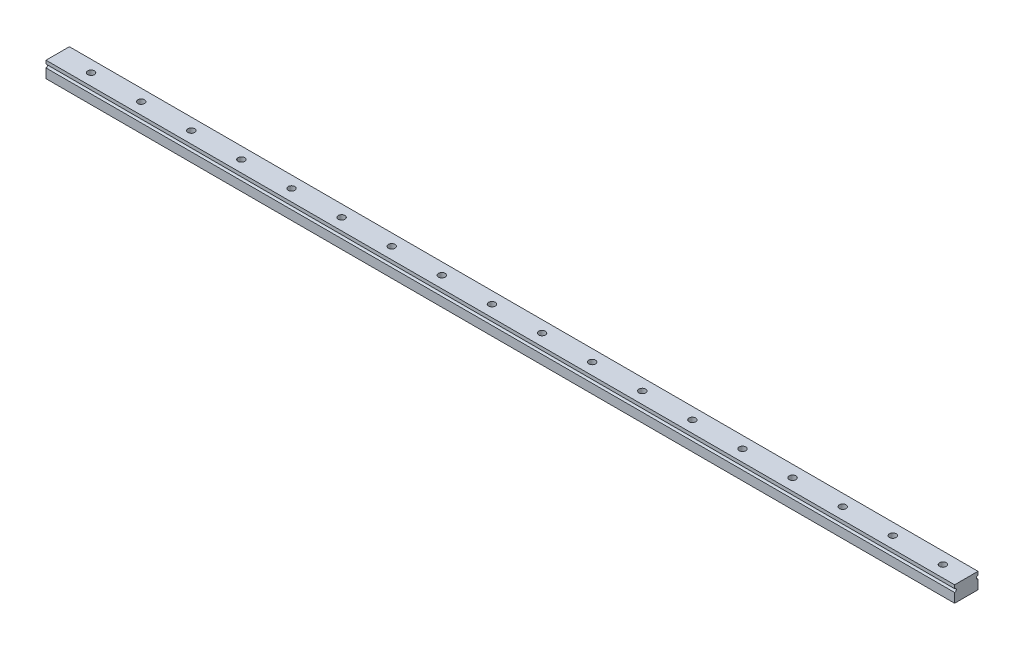
SolidWorks part; units mm, degrees
material "Plain Carbon Steel"
ref_plane "Front Plane" through (0, 0, 0) normal (0, 0, 1) x (1, 0, 0)
ref_plane "Top Plane" through (0, 0, 0) normal (0, 1, 0) x (1, 0, 0)
ref_plane "Right Plane" through (0, 0, 0) normal (1, 0, 0) x (0, 0, -1)
sketch "Sketch1" plane through (0, 0, 0) normal (1, 0, 0) x (0, 0, -1)
  line L1 (-3.5, 2.4) -> (3.5, 2.4)
  line L2 (-3.5, 2.4) -> (-3.5, -2.4)
  line L3 (-3.5, -2.4) -> (3.5, -2.4)
  line L4 (3.5, 2.4) -> (3.5, -2.4)
  line L5 (-3.5, 2.4) -> (3.5, -2.4) construction
  line L6 (-3.5, -2.4) -> (3.5, 2.4) construction
  circle A0 centre (-3.5, 0.9) radius 0.5
  circle A1 centre (3.5, 0.9) radius 0.5
  point P0 (0, 0)
  dimension "D3" = 1
  dimension "D4" = 1.5
  dimension "D1" = 4.8
  dimension "D2" = 7
extrude "Boss-Extrude1" add sketch "Sketch1" along normal blind 272 contours A1 L4 L1 L2 A0 L3
sketch "Sketch2" plane through (0, 2.4, 0) normal (0, 1, 0) x (1, 0, 0)
  line L0 (0, -3.5) -> (0, 3.5) construction
  circle A0 centre (10, 0) radius 1
  circle A1 centre (25, 0) radius 1
  circle A2 centre (40, 0) radius 1
  circle A3 centre (55, 0) radius 1
  circle A4 centre (70, 0) radius 1
  circle A5 centre (85, 0) radius 1
  circle A6 centre (100, 0) radius 1
  circle A7 centre (115, 0) radius 1
  circle A8 centre (130, 0) radius 1
  circle A9 centre (145, 0) radius 1
  circle A10 centre (160, 0) radius 1
  circle A11 centre (175, 0) radius 1
  circle A12 centre (190, 0) radius 1
  circle A13 centre (205, 0) radius 1
  circle A14 centre (220, 0) radius 1
  circle A15 centre (235, 0) radius 1
  circle A16 centre (250, 0) radius 1
  circle A17 centre (265, 0) radius 1
  circle A18 centre (280, 0) radius 1
  circle A19 centre (295, 0) radius 1
  circle A20 centre (310, 0) radius 1
  circle A21 centre (325, 0) radius 1
  circle A22 centre (340, 0) radius 1
  circle A23 centre (355, 0) radius 1
  circle A24 centre (370, 0) radius 1
  circle A25 centre (385, 0) radius 1
  circle A26 centre (400, 0) radius 1
  circle A27 centre (415, 0) radius 1
  circle A28 centre (430, 0) radius 1
  circle A29 centre (445, 0) radius 1
  circle A30 centre (460, 0) radius 1
  dimension "D1" = 10
  dimension "D2" = 2
  dimension "D4" = 15
  dimension "D3" = 31
extrude "Cut-Extrude1" cut sketch "Sketch2" against normal through all
